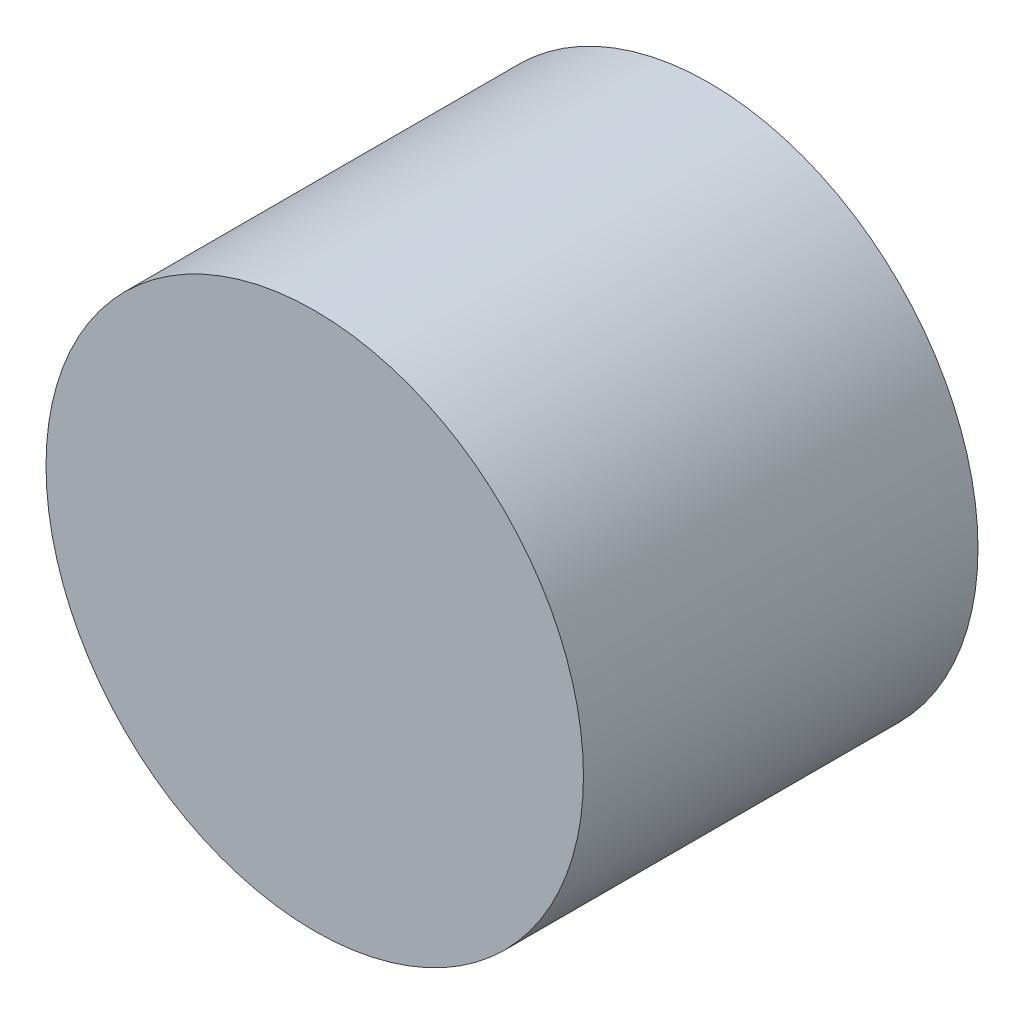
SolidWorks part; units mm, degrees
ref_plane "Front Plane" through (0, 0, 0) normal (0, 0, 1) x (1, 0, 0)
ref_plane "Top Plane" through (0, 0, 0) normal (0, 1, 0) x (1, 0, 0)
ref_plane "Right Plane" through (0, 0, 0) normal (1, 0, 0) x (0, 0, -1)
sketch "Sketch1" plane through (0, 0, 0) normal (0, 0, 1) x (1, 0, 0)
  circle A0 centre (4.2978, 0) radius 1.3623
extrude "Boss-Extrude1" add sketch "Sketch1" against normal up to surface (2 mm away)
equation "\"D6@Sketch1\"=\"D5@Sketch1\""
